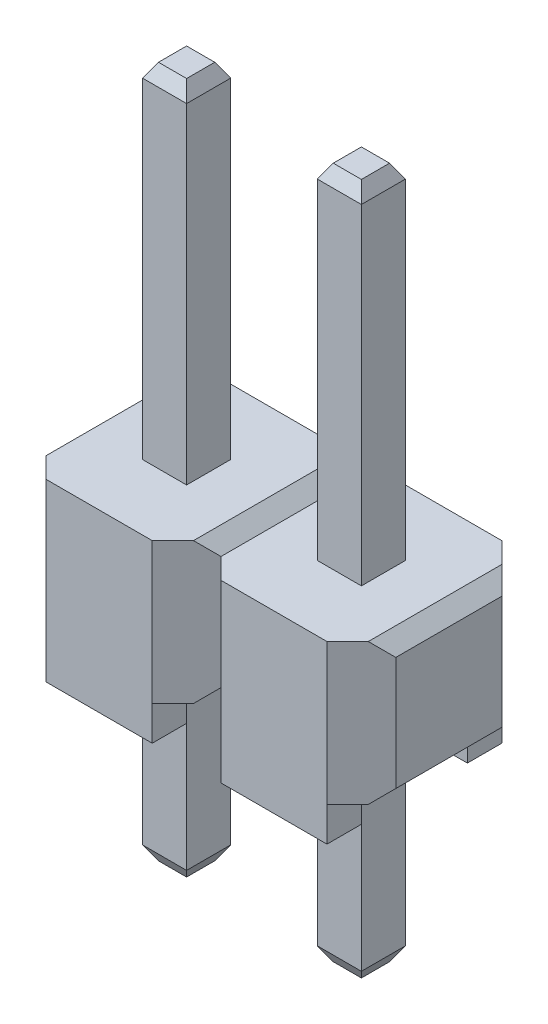
SolidWorks part; units mm, degrees
ref_plane "Front Plane" through (0, 0, 0) normal (0, 0, 1) x (1, 0, 0)
ref_plane "Top Plane" through (0, 0, 0) normal (0, 1, 0) x (1, 0, 0)
ref_plane "Right Plane" through (0, 0, 0) normal (1, 0, 0) x (0, 0, -1)
sketch "Sketch1" plane through (0, 0, 0) normal (0, 1, 0) x (1, 0, 0)
  line L0 (-2.04, -1.27) -> (-0.5, -1.27)
  line L1 (0, -0.77) -> (-0.5, -1.27)
  line L2 (0.5, -1.27) -> (2.04, -1.27)
  line L3 (-55, 0) -> (55, 0) construction
  line L4 (-2.54, 0) -> (-1.59, 0) construction
  line L5 (-1.59, 0) -> (-0.95, 0) construction
  line L6 (-0.95, 0) -> (0.95, 0) construction
  line L7 (0.95, 0) -> (1.59, 0) construction
  line L8 (1.59, 0) -> (2.54, 0) construction
  line L9 (-1.27, 1.27) -> (-1.27, 0.32) construction
  line L10 (-1.27, 0.32) -> (-1.27, -0.32) construction
  line L11 (-1.27, -0.32) -> (-1.27, -1.27) construction
  line L12 (0, 0.77) -> (0, 0) construction
  line L13 (0, 0) -> (0, -0.77) construction
  line L22 (1.59, -0.32) -> (1.59, 0.32)
  line L34 (0, -55) -> (0, 55) construction
  line L44 (-2.04, 1.27) -> (-0.5, 1.27)
  line L45 (-0.5, 1.27) -> (0, 0.77)
  line L46 (-1.59, -0.32) -> (-1.59, 0.32)
  line L47 (0.95, -0.32) -> (1.59, -0.32)
  line L48 (2.54, 0.77) -> (2.54, -0.77)
  line L49 (-2.04, -1.27) -> (-2.54, -0.77)
  line L51 (-1.59, -0.32) -> (-0.95, -0.32)
  line L53 (0, 0.77) -> (0.5, 1.27)
  line L54 (2.54, -0.77) -> (2.04, -1.27)
  line L55 (2.04, 1.27) -> (2.54, 0.77)
  line L56 (0.95, 0.32) -> (1.59, 0.32)
  line L57 (-2.54, 0.77) -> (-2.04, 1.27)
  line L58 (-2.54, -0.77) -> (-2.54, 0.77)
  line L59 (-1.59, 0.32) -> (-0.95, 0.32)
  line L60 (-0.95, -0.32) -> (-0.95, 0.32)
  line L61 (0.5, -1.27) -> (0, -0.77)
  line L62 (0.5, 1.27) -> (2.04, 1.27)
  line L63 (0.95, -0.32) -> (0.95, 0.32)
  dimension "D1" = 5.08
  dimension "D2" = 2.54
  dimension "D3" = 1.27
  dimension "D4" = 2.54
  dimension "D5" = 0.64
  dimension "D7" = 0.5
  dimension "D10" = 0.5
  dimension "D11" = 1.54
extrude "Boss-Extrude1" add sketch "Sketch1" against normal blind 2.05
sketch "Sketch2" plane through (0, 0, 0) normal (0, 0, 1) x (1, 0, 0)
  line L0 (-2.54, -0.2) -> (-2.54, 0)
  line L3 (-2.54, -2.05) -> (-2.54, 0) construction
  line L4 (-2.54, 0) -> (-2.34, 0)
  line L5 (-2.54, 0) -> (-2.04, 0) construction
  line L8 (-2.34, 0) -> (-2.54, -0.2)
  line L10 (-0.2, 0) -> (0.2, 0)
  line L11 (-0.5, 0) -> (0, 0) construction
  line L13 (0, 0) -> (0.5, 0) construction
  line L15 (0.2, 0) -> (0, -0.2)
  line L16 (0, -2.05) -> (0, 0) construction
  line L17 (0, -0.2) -> (-0.2, 0)
  line L18 (2.34, 0) -> (2.54, 0)
  line L19 (2.04, 0) -> (2.54, 0) construction
  line L20 (2.54, 0) -> (2.54, -0.2)
  line L21 (2.54, -2.05) -> (2.54, 0) construction
  line L22 (2.54, -0.2) -> (2.34, 0)
  line L23 (-2.54, -1.85) -> (-2.34, -2.05)
  line L24 (-2.54, -2.05) -> (-2.04, -2.05) construction
  line L25 (-2.34, -2.05) -> (-2.54, -2.05)
  line L26 (-2.54, -2.05) -> (-2.54, -1.85)
  line L27 (-0.2, -2.05) -> (0, -1.85)
  line L28 (-0.5, -2.05) -> (0, -2.05) construction
  line L29 (0, -1.85) -> (0.2, -2.05)
  line L31 (0.2, -2.05) -> (-0.2, -2.05)
  line L32 (2.34, -2.05) -> (2.54, -1.85)
  line L34 (2.54, -1.85) -> (2.54, -2.05)
  line L35 (2.54, -2.05) -> (2.34, -2.05)
  dimension "D1" = 0.2
  dimension "D2" = 0.4
extrude "Cut-Extrude1" cut sketch "Sketch2" against normal mid plane 10
sketch "Sketch3" plane through (0, -2.05, 0) normal (0, -1, 0) x (1, 0, 0)
  line L2 (-2.04, -1.27) -> (-0.5, -1.27)
  line L3 (-2.04, -1.27) -> (-2.04, -0.77)
  line L4 (-2.04, -0.77) -> (-0.5, -0.77)
  line L5 (-0.5, -1.27) -> (-0.5, -0.77)
  line L6 (-0.5, 1.27) -> (-2.04, 1.27)
  line L7 (-0.5, 1.27) -> (-0.5, 0.77)
  line L8 (-0.5, 0.77) -> (-2.04, 0.77)
  line L9 (-2.04, 1.27) -> (-2.04, 0.77)
  line L10 (0.5, 1.27) -> (2.04, 1.27)
  line L11 (0.5, 1.27) -> (0.5, 0.77)
  line L12 (0.5, 0.77) -> (2.04, 0.77)
  line L13 (2.04, 1.27) -> (2.04, 0.77)
  line L14 (2.04, -1.27) -> (0.5, -1.27)
  line L15 (2.04, -1.27) -> (2.04, -0.77)
  line L16 (2.04, -0.77) -> (0.5, -0.77)
  line L17 (0.5, -1.27) -> (0.5, -0.77)
  dimension "D1" = 0.5
extrude "Boss-Extrude2" add sketch "Sketch3" along normal blind 0.5
sketch "Sketch4" plane through (0, 0, 0) normal (0, 1, 0) x (1, 0, 0)
  line L1 (-1.59, 0.32) -> (-0.95, 0.32)
  line L2 (-1.59, 0.32) -> (-1.59, -0.32)
  line L3 (-1.59, -0.32) -> (-0.95, -0.32)
  line L4 (-0.95, 0.32) -> (-0.95, -0.32)
  line L5 (0.95, 0.32) -> (1.59, 0.32)
  line L6 (0.95, 0.32) -> (0.95, -0.32)
  line L7 (0.95, -0.32) -> (1.59, -0.32)
  line L8 (1.59, 0.32) -> (1.59, -0.32)
extrude "Boss-Extrude3" add sketch "Sketch4" along normal blind 5 and the other way offset from surface (5.05 mm away) 3 other way up to face at (1.27, -2.05, 0)
chamfer "Chamfer1" distance 0.2 angle 30 16 edges at (-1.27, -5.05, 0.32) (-0.95, -5.05, 0) (-1.27, -5.05, -0.32) (-1.59, -5.05, 0) (1.27, -5.05, 0.32) (1.59, -5.05, 0) (1.27, -5.05, -0.32) (0.95, -5.05, 0) (1.27, 5, -0.32) (1.59, 5, 0) (1.27, 5, 0.32) (0.95, 5, 0) (-1.27, 5, -0.32) (-0.95, 5, 0) (-1.27, 5, 0.32) (-1.59, 5, 0)
sketch "Sketch5" plane through (0, -5.05, 0) normal (0, -1, 0) x (1, 0, 0)
  line L0 (-1.59, 0) -> (-0.95, 0) construction
  line L1 (-1.59, -0.32) -> (-1.59, 0.32) construction
  line L2 (-0.95, 0.32) -> (-0.95, -0.32) construction
  circle A0 centre (-1.27, 0) radius 0.125
  dimension "D1" = 0.25
extrude "Cut-Extrude2" cut sketch "Sketch5" against normal blind 1
